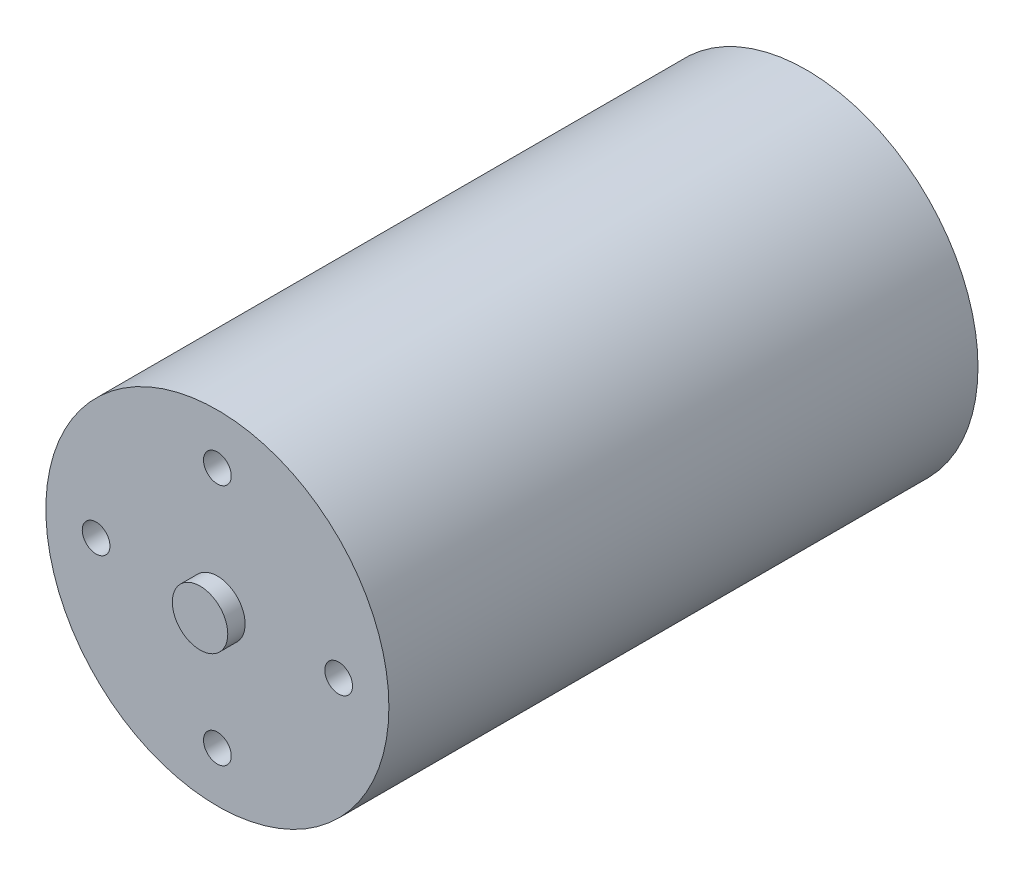
SolidWorks part; units mm, degrees
ref_plane "Front Plane" through (0, 0, 0) normal (0, 0, 1) x (1, 0, 0)
ref_plane "Top Plane" through (0, 0, 0) normal (0, 1, 0) x (1, 0, 0)
ref_plane "Right Plane" through (0, 0, 0) normal (1, 0, 0) x (0, 0, -1)
sketch "Sketch1" plane through (0, 0, 0) normal (0, 0, 1) x (1, 0, 0)
  circle A0 centre (0, 0) radius 24.75
  dimension "D1" = 49.5
extrude "Boss-Extrude1" add sketch "Sketch1" against normal mid plane 85
sketch "Sketch2" plane through (0, 0, 42.5) normal (0, 0, 1) x (1, 0, 0)
  circle A0 centre (0, 0) radius 4
  dimension "D1" = 8
extrude "Boss-Extrude2" add sketch "Sketch2" along normal blind 2.5
sketch "Sketch6" plane through (0, 0, 42.5) normal (0, 0, 1) x (1, 0, 0)
  circle A0 centre (0, 0) radius 17.5 construction
  circle A1 centre (0, 17.5) radius 2
  dimension "D1" = 4
  dimension "D5" = 35
extrude "Cut-Extrude3" cut sketch "Sketch6" against normal blind 5
pattern_circular "CirPattern1" count 4 over 360 about axis through (0, 0, 0) along (0, 0, 1) of "Cut-Extrude3"
sketch "Sketch5" plane through (0, 0, -42.5) normal (0, 0, -1) x (-1, 0, 0)
  circle A0 centre (0, 0) radius 17.5 construction
  circle A1 centre (-17.5, 0) radius 2
  dimension "D1" = 35
  dimension "D2" = 4
extrude "Cut-Extrude2" cut sketch "Sketch5" against normal blind 10
pattern_circular "CirPattern2" count 4 over 360 about axis through (0, 0, 0) along (0, 0, 1) of "Cut-Extrude2"
sketch "Sketch7" plane through (0, 0, -42.5) normal (0, 0, -1) x (-1, 0, 0)
  circle A0 centre (0, 0) radius 10.5
  dimension "D1" = 21
extrude "Boss-Extrude3" add sketch "Sketch7" along normal blind 5
